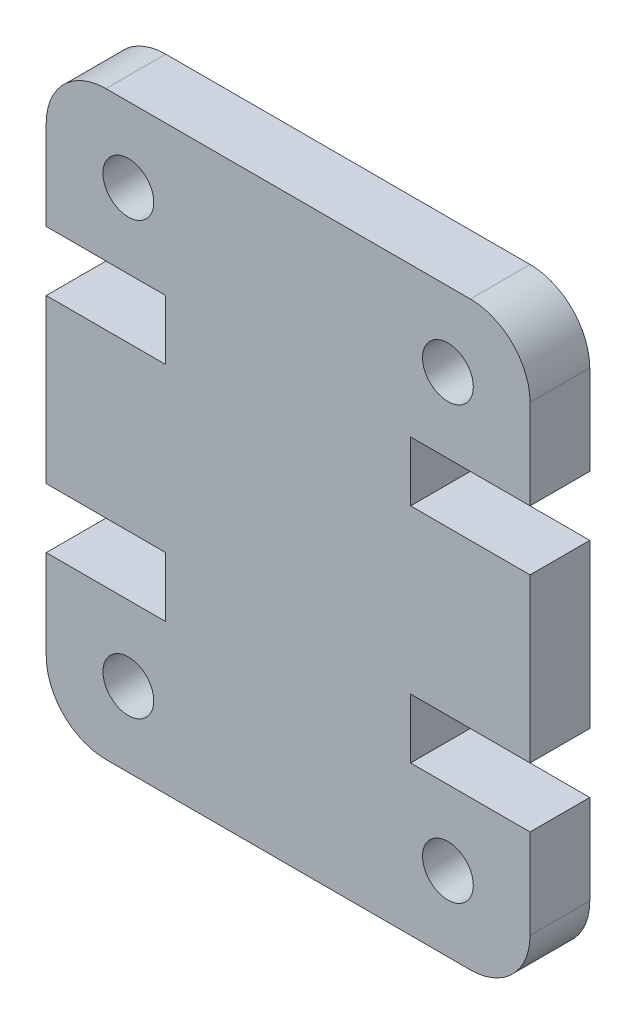
SolidWorks part; units mm, degrees
ref_plane "Front Plane" through (0, 0, 0) normal (0, 0, 1) x (1, 0, 0)
ref_plane "Top Plane" through (0, 0, 0) normal (0, 1, 0) x (1, 0, 0)
ref_plane "Right Plane" through (0, 0, 0) normal (1, 0, 0) x (0, 0, -1)
sketch "Sketch2" plane through (0, 0, 0) normal (0, 0, 1) x (1, 0, 0)
  line L0 (0, 7) -> (0, 12.455)
  line L1 (2, 0) -> (14.2, 0)
  line L2 (16.2, 5) -> (16.2, 2)
  line L3 (0, 9.7275) -> (16.2, 9.7275) construction
  line L4 (12.2, 5) -> (16.2, 5)
  line L5 (16.2, 7) -> (12.2, 7)
  line L6 (12.2, 7) -> (12.2, 5)
  line L7 (16.2, 7) -> (16.2, 12.455)
  line L8 (4, 7) -> (4, 5)
  line L9 (0, 14.455) -> (0, 17.455)
  line L10 (0, 7) -> (4, 7)
  line L11 (4, 5) -> (0, 5)
  line L12 (4, 14.455) -> (0, 14.455)
  line L13 (0, 12.455) -> (4, 12.455)
  line L14 (4, 12.455) -> (4, 14.455)
  line L15 (12.2, 12.455) -> (12.2, 14.455)
  line L16 (16.2, 12.455) -> (12.2, 12.455)
  line L17 (12.2, 14.455) -> (16.2, 14.455)
  line L18 (16.2, 14.455) -> (16.2, 17.455)
  line L19 (0, 5) -> (0, 2)
  line L20 (8.1, 19.455) -> (8.1, 0) construction
  line L21 (2, 19.455) -> (14.2, 19.455)
  circle A0 centre (13.45, 2.5) radius 0.85
  arc A1 (16.2, 2) -> (14.2, 0) centre (14.2, 2) cw
  circle A2 centre (2.75, 16.955) radius 0.85
  arc A3 (0, 2) -> (2, 0) centre (2, 2) ccw
  arc A4 (0, 17.455) -> (2, 19.455) centre (2, 17.455) cw
  circle A5 centre (2.75, 2.5) radius 0.85
  arc A6 (16.2, 17.455) -> (14.2, 19.455) centre (14.2, 17.455) ccw
  circle A7 centre (13.45, 16.955) radius 0.85
  point P18 (8.1, 9.7275)
  dimension "D1" = 1.7
  dimension "D2" = 2
  dimension "D3" = 2.75
  dimension "D4" = 8.1
  dimension "D5" = 2.5
  dimension "D6" = 5
  dimension "D8" = 9.7275
extrude "Boss-Extrude1" add sketch "Sketch2" along normal blind 4
sketch "Sketch3" plane through (0, 0, 4) normal (0, 0, 1) x (1, 0, 0)
  line L0 (0, 0) -> (16.2, 0)
  line L1 (16.2, 0) -> (16.2, 19.455)
  line L2 (16.2, 19.455) -> (0, 19.455)
  line L3 (0, 19.455) -> (0, 0)
extrude "Cut-Extrude1" cut sketch "Sketch3" against normal blind 2
equation "\"D4@Sketch2\"= \"fingerWidth@parametersSketch@prostheticParameters.SLDPRT\" / 2'Finger Width"
equation "\"D8@Sketch2\"= ( ( \"HL@parametersSketch@prostheticParameters.SLDPRT\" * 0.143 ) - 3 - 4 ) / 2 'MIP Length -SiliconeDIP-SiliconeMIP"
equation "\"D1@Sketch2\"= 1.5 + \"tol1@parametersSketch@prostheticParameters.SLDPRT\""
